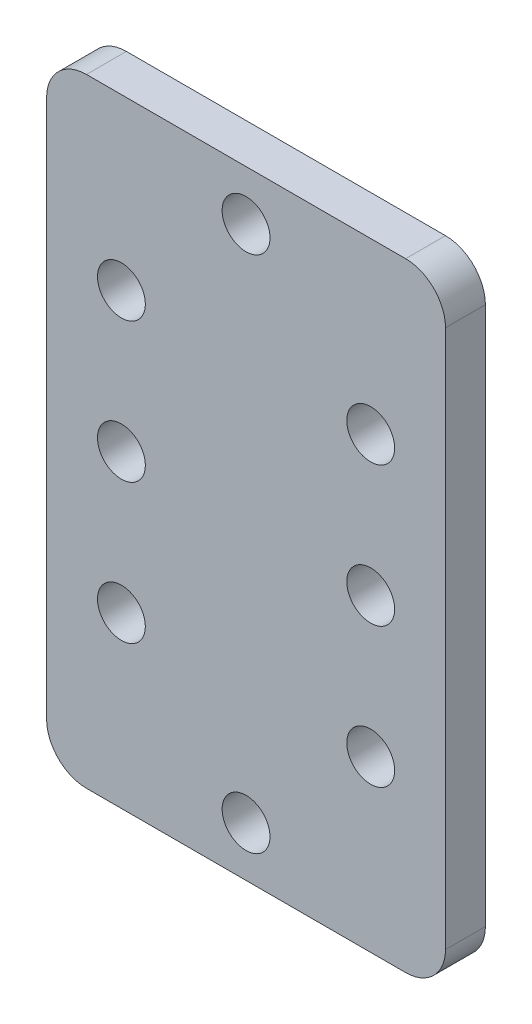
SolidWorks part; units mm, degrees
ref_plane "Front Plane" through (0, 0, 0) normal (0, 0, 1) x (1, 0, 0)
ref_plane "Top Plane" through (0, 0, 0) normal (0, 1, 0) x (1, 0, 0)
ref_plane "Right Plane" through (0, 0, 0) normal (1, 0, 0) x (0, 0, -1)
sketch "Sketch1" plane through (0, 0, 0) normal (0, 0, 1) x (1, 0, 0)
  line L0 (12.7, -3.175) -> (12.7, -36.195) construction
  line L1 (0, 0) -> (25.4, 0)
  line L2 (0, 0) -> (0, -39.37)
  line L3 (0, -39.37) -> (25.4, -39.37)
  line L4 (25.4, 0) -> (25.4, -39.37)
  line L5 (0, -19.685) -> (25.4, -19.685) construction
  circle A0 centre (4.7625, -19.685) radius 1.524
  circle A1 centre (20.6375, -19.685) radius 1.524
  circle A2 centre (4.7625, -10.795) radius 1.524
  circle A3 centre (20.6375, -10.795) radius 1.524
  circle A4 centre (4.7625, -28.575) radius 1.524
  circle A5 centre (20.6375, -28.575) radius 1.524
  circle A6 centre (12.7, -3.175) radius 1.524
  circle A7 centre (12.7, -36.195) radius 1.524
  point P6 (12.7, -19.685)
  dimension "D3" = 3.048
  dimension "D7" = 3.048
  dimension "D1" = 39.37
  dimension "D2" = 25.4
  dimension "D4" = 15.875
  dimension "D8" = 33.02
  dimension "D5" = 2
  dimension "D6" = 2
extrude "Boss-Extrude1" add sketch "Sketch1" along normal blind 2.54
fillet "Fillet1" radius 2.54 4 edges at (25.4, -39.37, 1.27) (25.4, 0, 1.27) (0, -39.37, 1.27) (0, 0, 1.27)
